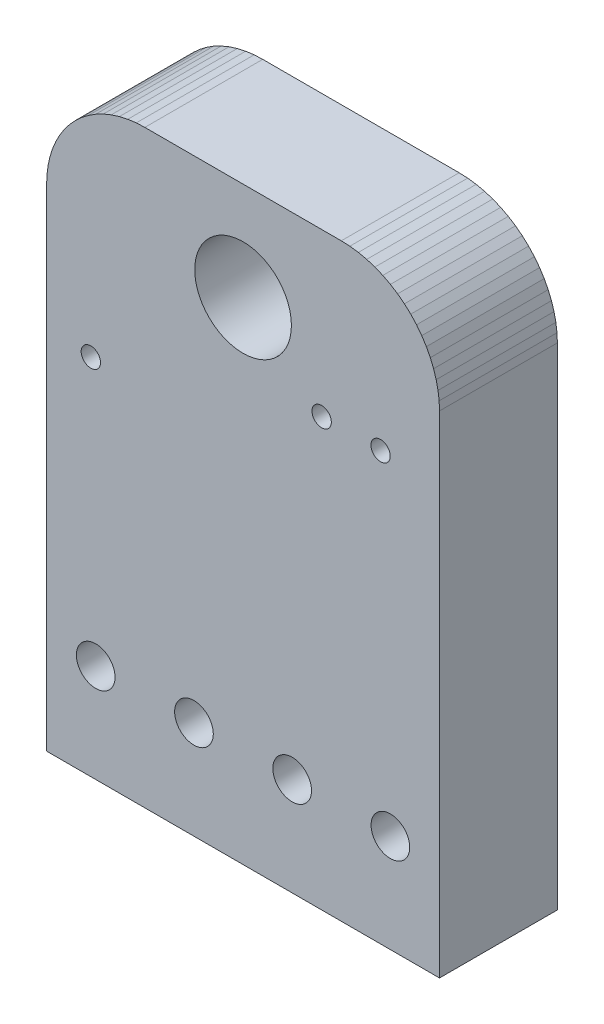
SolidWorks part; units mm, degrees
ref_plane "Front Plane" through (0, 0, 0) normal (0, 0, 1) x (1, 0, 0)
ref_plane "Top Plane" through (0, 0, 0) normal (0, 1, 0) x (1, 0, 0)
ref_plane "Right Plane" through (0, 0, 0) normal (1, 0, 0) x (0, 0, -1)
sketch "Model" plane through (0, 0, 0) normal (0, 0, 1) x (1, 0, 0)
  line L0 (0, 0) -> (10, 0)
  line L1 (10, 0) -> (10, 12.5)
  line L2 (10, 12.5) -> (9.9905, 12.7179)
  line L3 (9.9905, 12.7179) -> (9.962, 12.9341)
  line L4 (9.962, 12.9341) -> (9.9148, 13.147)
  line L5 (9.9148, 13.147) -> (9.8492, 13.3551)
  line L6 (9.8492, 13.3551) -> (9.7658, 13.5565)
  line L7 (9.7658, 13.5565) -> (9.6651, 13.75)
  line L8 (9.6651, 13.75) -> (9.5479, 13.9339)
  line L9 (9.5479, 13.9339) -> (9.4151, 14.107)
  line L10 (9.4151, 14.107) -> (9.2678, 14.2678)
  line L11 (9.2678, 14.2678) -> (9.107, 14.4151)
  line L12 (9.107, 14.4151) -> (8.9339, 14.5479)
  line L13 (8.9339, 14.5479) -> (8.75, 14.6651)
  line L14 (8.75, 14.6651) -> (8.5565, 14.7658)
  line L15 (8.5565, 14.7658) -> (8.3551, 14.8492)
  line L16 (8.3551, 14.8492) -> (8.147, 14.9148)
  line L17 (8.147, 14.9148) -> (7.9341, 14.962)
  line L18 (7.9341, 14.962) -> (7.7179, 14.9905)
  line L19 (7.7179, 14.9905) -> (7.5, 15)
  line L20 (7.5, 15) -> (2.5, 15)
  line L21 (2.5, 15) -> (2.2821, 14.9905)
  line L22 (2.2821, 14.9905) -> (2.0659, 14.962)
  line L23 (2.0659, 14.962) -> (1.853, 14.9148)
  line L24 (1.853, 14.9148) -> (1.6449, 14.8492)
  line L25 (1.6449, 14.8492) -> (1.4435, 14.7658)
  line L26 (1.4435, 14.7658) -> (1.25, 14.6651)
  line L27 (1.25, 14.6651) -> (1.0661, 14.5479)
  line L28 (1.0661, 14.5479) -> (0.893, 14.4151)
  line L29 (0.893, 14.4151) -> (0.7322, 14.2678)
  line L30 (0.7322, 14.2678) -> (0.5849, 14.107)
  line L31 (0.5849, 14.107) -> (0.4521, 13.9339)
  line L32 (0.4521, 13.9339) -> (0.3349, 13.75)
  line L33 (0.3349, 13.75) -> (0.2342, 13.5565)
  line L34 (0.2342, 13.5565) -> (0.1508, 13.3551)
  line L35 (0.1508, 13.3551) -> (0.0852, 13.147)
  line L36 (0.0852, 13.147) -> (0.038, 12.9341)
  line L37 (0.038, 12.9341) -> (0.0095, 12.7179)
  line L38 (0.0095, 12.7179) -> (0, 12.5)
  line L39 (0, 12.5) -> (0, 0)
  circle A0 centre (5, 12.5) radius 1.2303
  circle A1 centre (8.75, 2.5) radius 0.4921
  circle A2 centre (6.25, 2.5) radius 0.4921
  circle A3 centre (3.75, 2.5) radius 0.4921
  circle A4 centre (1.25, 2.5) radius 0.4921
  circle A5 centre (1.125, 9.25) radius 0.2461
  circle A6 centre (8.5, 10.875) radius 0.2461
  circle A7 centre (7, 10.875) radius 0.2461
  dimension "D1" = 10
  dimension "D2" = 15
extrude "Boss-Extrude1" add sketch "Model" along normal blind 3
